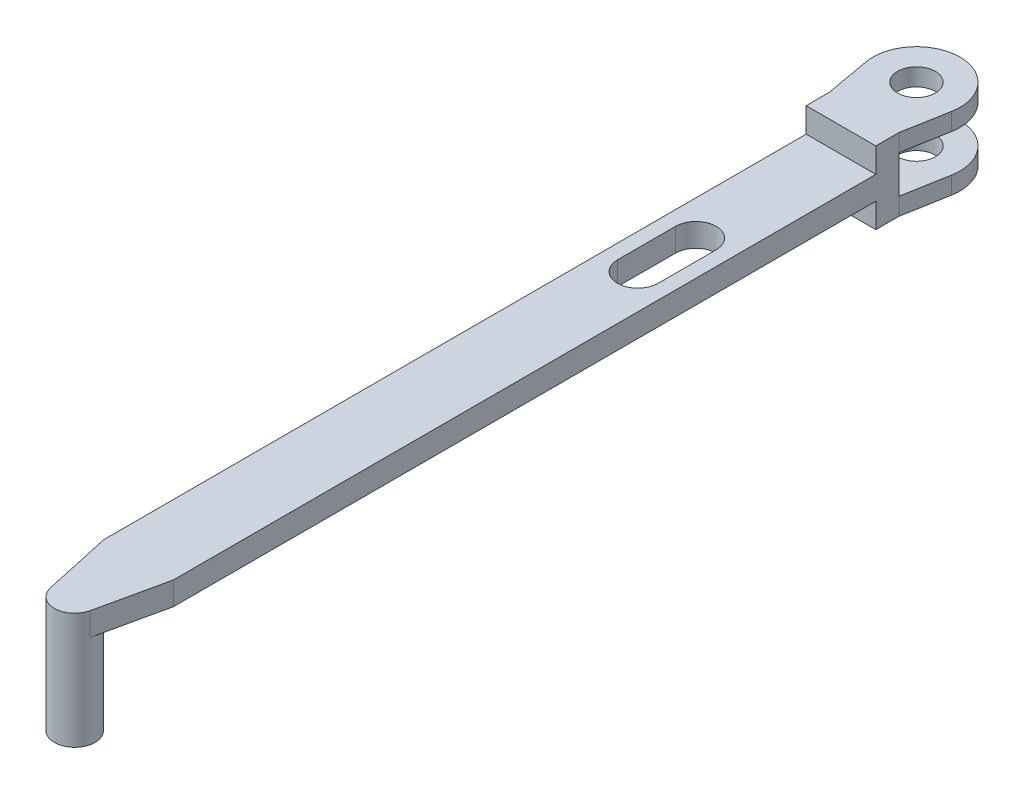
SolidWorks part; units mm, degrees
ref_plane "Спереди" through (0, 0, 0) normal (0, 0, 1) x (1, 0, 0)
ref_plane "Сверху" through (0, 0, 0) normal (0, 1, 0) x (1, 0, 0)
ref_plane "Справа" through (0, 0, 0) normal (1, 0, 0) x (0, 0, -1)
other "Configuration Table"
sketch "Эскиз1" plane through (0, 0, 0) normal (0, 1, 0) x (1, 0, 0)
  line L0 (0, 16.6919) -> (0, -19.5386) construction
  line L1 (-7.3813, -1.3291) -> (-6, -9)
  line L2 (-6, -9) -> (6, -9)
  line L3 (6, -9) -> (7.3813, -1.3291)
  arc A0 (7.3813, -1.3291) -> (-7.3813, -1.3291) centre (0, 0) ccw
  point P7 (0, 0)
  dimension "D1" = 15
  dimension "D2" = 12
  dimension "D3" = 9
extrude "Бобышка-Вытянуть1" add sketch "Эскиз1" along normal blind 3
sketch "Эскиз2" plane through (0, 0, 9) normal (0, 0, 1) x (1, 0, 0)
  line L1 (-6, 0) -> (6, 0)
  line L2 (-6, 0) -> (-6, 12.5)
  line L3 (-6, 12.5) -> (6, 12.5)
  line L4 (6, 0) -> (6, 12.5)
  dimension "D1" = 12
  dimension "D2" = 12.5
extrude "Бобышка-Вытянуть2" add sketch "Эскиз2" along normal blind 4
sketch "Эскиз3" plane through (0, 12.5, 0) normal (0, 1, 0) x (1, 0, 0)
  line L3 (-7.3813, -1.3291) -> (-6, -9)
  line L4 (-6, -9) -> (6, -9)
  line L5 (6, -9) -> (7.3813, -1.3291)
  line L6 (-7.3813, -1.3291) -> (-6, -9)
  line L7 (-6, -9) -> (6, -9)
  line L8 (6, -9) -> (7.3813, -1.3291)
  arc A1 (7.3813, -1.3291) -> (-7.3813, -1.3291) centre (0, 0) ccw
  arc A2 (7.3813, -1.3291) -> (-7.3813, -1.3291) centre (0, 0) ccw
  dimension "D1" = 0
extrude "Бобышка-Вытянуть3" add sketch "Эскиз3" against normal blind 3
sketch "Эскиз4" plane through (0, 12.5, 0) normal (0, 1, 0) x (1, 0, 0)
  circle A0 centre (0, 0) radius 3.25
  dimension "D1" = 6.5
extrude "Вырез-Вытянуть1" cut sketch "Эскиз4" against normal through all
ref_plane "Плоскость2" through (0, 6.25, 0) normal (0, 1, 0) x (1, 0, 0)
sketch "Эскиз5" plane through (0, 6.25, 0) normal (0, 1, 0) x (1, 0, 0)
  line L1 (-6, -13) -> (6, -13)
  line L2 (-6, -13) -> (-6, -134.0062)
  line L4 (6, -13) -> (6, -134.0062)
  line L6 (0, 0) -> (0, -62.4101) construction
  line L7 (3.5, -38) -> (3.5, -48)
  line L8 (-3.5, -38) -> (-3.5, -48)
  line L9 (3.4184, -145.7514) -> (6, -134.0062)
  line L10 (-3.4184, -145.7514) -> (-6, -134.0062)
  arc A2 (3.5, -38) -> (-3.5, -38) centre (0, -38) ccw
  arc A3 (-3.5, -48) -> (3.5, -48) centre (0, -48) ccw
  arc A4 (-3.4184, -145.7514) -> (3.4184, -145.7514) centre (0, -145) ccw
  dimension "D1" = 7
  dimension "D2" = 7
  dimension "D5" = 7
  dimension "D3" = 10
  dimension "D4" = 38
  dimension "D6" = 12
  dimension "D7" = 11.7452
  dimension "D8" = 145
  dimension "D9" = 167.603
  dimension "D10" = 167.603
extrude "Бобышка-Вытянуть4" add sketch "Эскиз5" along normal blind 2 and the other way blind 2
sketch "Эскиз6" plane through (0, 8.25, 0) normal (0, 1, 0) x (1, 0, 0)
  circle A0 centre (0, -145) radius 3.5
extrude "Бобышка-Вытянуть5" add sketch "Эскиз6" against normal blind 20
